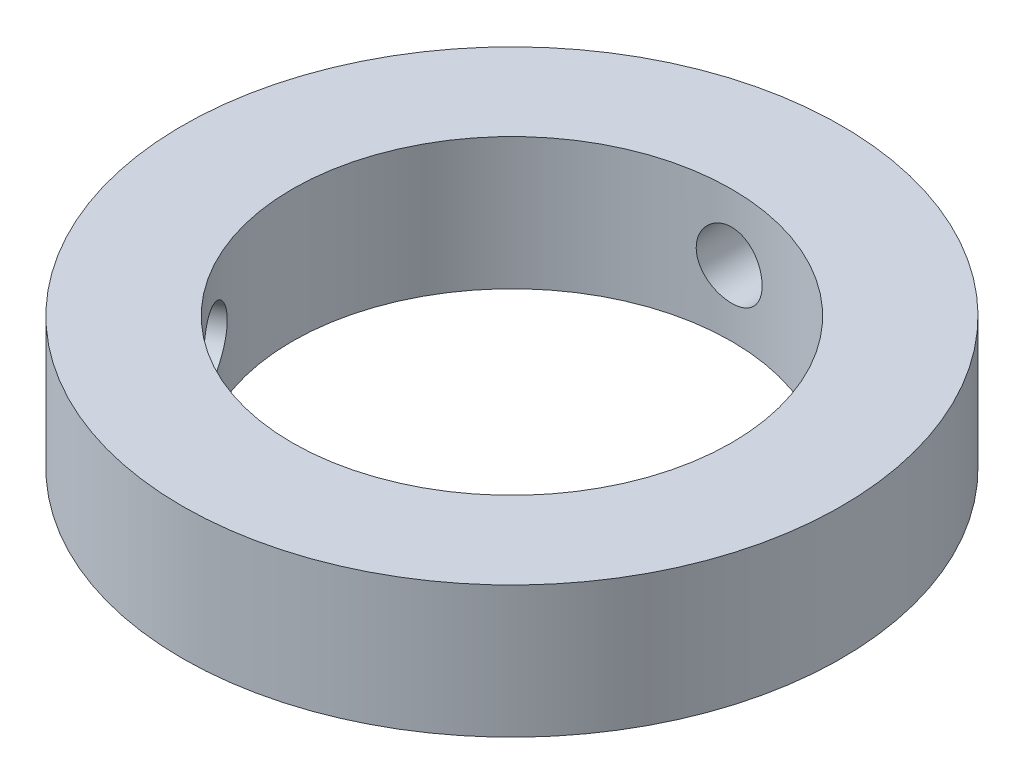
SolidWorks part; units mm, degrees
ref_plane "정면" through (0, 0, 0) normal (0, 0, 1) x (1, 0, 0)
ref_plane "윗면" through (0, 0, 0) normal (0, 1, 0) x (1, 0, 0)
ref_plane "우측면" through (0, 0, 0) normal (1, 0, 0) x (0, 0, -1)
sketch "스케치1" plane through (0, 0, 0) normal (0, 1, 0) x (1, 0, 0)
  circle A0 centre (0, 0) radius 10
  circle A1 centre (0, 0) radius 15
  dimension "D1" = 20
  dimension "D2" = 30
extrude "보스-돌출1" add sketch "스케치1" along normal blind 6
ref_plane "평면1" through (0, 0, -15) normal (0, 0, -1) x (-1, 0, 0)
ref_plane "평면2" through (-12.9904, 0, 7.5) normal (-0.866, 0, 0.5) x (0, -1, 0)
sketch "스케치2" plane through (0, 0, -15) normal (0, 0, -1) x (-1, 0, 0)
  line L0 (0, 3.3) -> (0, -3.3) construction
  line L1 (15, 6) -> (-15, 6) construction
  circle A0 centre (0, 3) radius 1.5
  point P2 (0, 0)
  dimension "D1" = 3
  dimension "D2" = 3
extrude "컷-돌출1" cut sketch "스케치2" against normal up to next
sketch "스케치3" plane through (-12.9904, 0, 7.5) normal (-0.866, 0, 0.5) x (0, -1, 0)
  line L0 (-6, 15) -> (-6, -15) construction
  line L1 (0, 15) -> (-6, 15) construction
  circle A0 centre (-3, 0) radius 1.5
  point P2 (0, 0)
  point P3 (-2.9213, 0)
  point P4 (0, 0)
  dimension "D1" = 3
  dimension "D2" = 3
  dimension "D3" = 15
extrude "컷-돌출2" cut sketch "스케치3" against normal up to next
